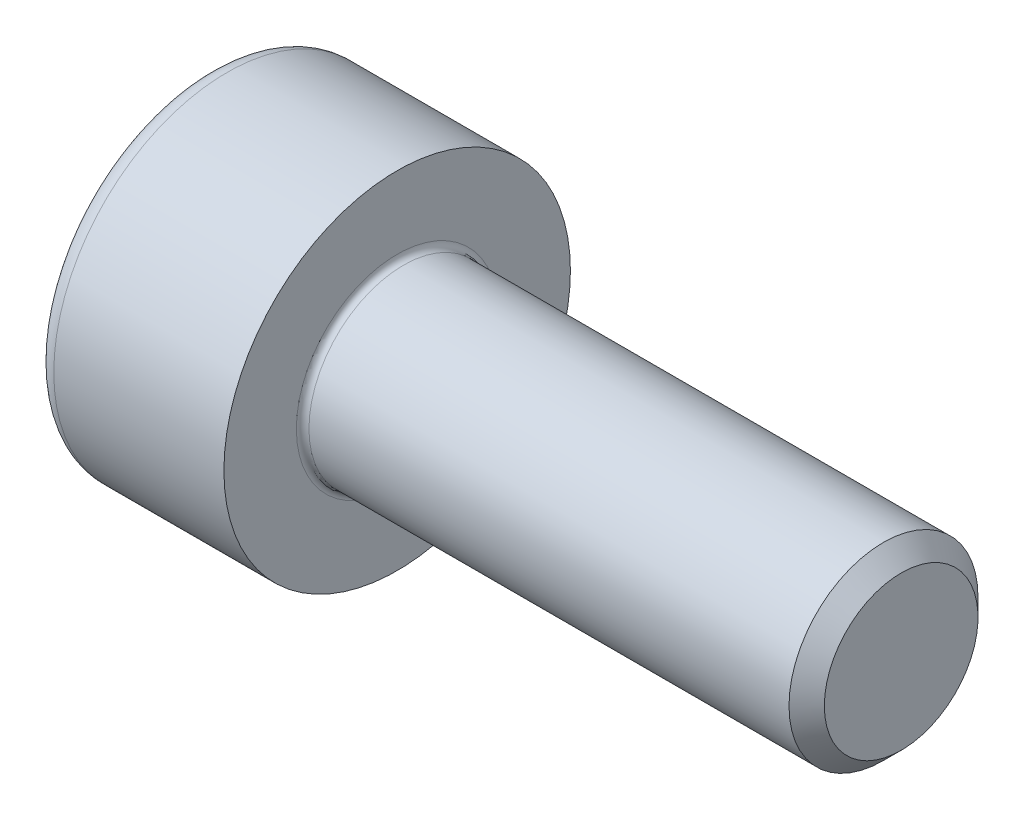
SolidWorks part; units mm, degrees
revolve "Base-Revolve" add sketch "BodySke"
sketch "BodySke" plane through (0, 0, 0) normal (0, 0, 1) x (1, 0, 0)
  line L0 (0, 0) -> (0, 2.75)
  line L1 (0, 2.75) -> (3, 2.75)
  line L2 (3, 2.75) -> (3, 1.5)
  line L3 (3, 1.5) -> (10.7195, 1.5)
  line L4 (11, 1.2195) -> (11, 0)
  line L5 (11, 0) -> (0, 0)
  line L6 (-31.75, 0) -> (127, 0) construction
  line L8 (11, 1.2195) -> (10.7195, 1.5)
  line L10 (11, -1.2195) -> (10.7195, -1.5) construction
  line L11 (3.5, 9.525) -> (3.5, 3.175) construction
  line L12 (3, 9.525) -> (3, 3.175) construction
  line L13 (-49, 9.525) -> (-49, 3.175) construction
  dimension "Head_ht" = 3
  dimension "Length" = 8
  dimension "Body_ch_ang" = 45
  dimension "Diameter" = 3
  dimension "Minor_dia" = 2.439
  dimension "Advance" = 0.5
  dimension "Thread_nom" = 8
  dimension "Thread_length" = 60
  dimension "Head_dia" = 5.5
cosmetic thread "ThreadCosmetic"
fillet "Fillet1" radius 0.1 1 edges at (3, 0, 1.5)
fillet "Fillet2" radius 0.3 1 edges at (0, 0, 2.75)
ref_plane "Plane1" through (0, 0, 0) normal (0, 0, 1) x (1, 0, 0)
ref_plane "Plane2" through (0, 0, 0) normal (0, 1, 0) x (1, 0, 0)
ref_plane "Plane3" through (0, 0, 0) normal (1, 0, 0) x (0, 0, -1)
sketch "Sketch2" plane through (0, 0, 0) normal (0, 0, 1) x (1, 0, 0)
  line L0 (0, 1.26) -> (1.3, 1.26)
  line L1 (1.3, 1.26) -> (2.0275, 0)
  line L2 (-31.75, 0) -> (127, 0) construction
  line L3 (2.0275, 0) -> (0, 0)
  line L4 (0, 0) -> (0, 1.26)
  line L6 (0, 0) -> (47.625, 0) construction
  dimension "D1" = 1.26
  dimension "D2" = 60
  dimension "Depth" = 1.3
revolve "Hex-PreBroach" cut sketch "Sketch2" angle 360 about L6
sketch "Sketch3" plane through (0, 0, 0) normal (-1, 0, 0) x (0, 0.5, 0.866)
  line L0 (0.7275, 1.26) -> (-0.7275, 1.26)
  line L1 (-0.7275, 1.26) -> (-1.4549, 0)
  line L2 (0.7275, 1.26) -> (1.4549, 0)
  line L3 (0.7275, -1.26) -> (1.4549, 0)
  line L4 (0.7275, -1.26) -> (-0.7275, -1.26)
  line L5 (-0.7275, -1.26) -> (-1.4549, 0)
  dimension "D1" = 1.26
  dimension "D2" = 1.26
  dimension "Hex_size" = 2.52
extrude "Hex" cut sketch "Sketch3" against normal blind 1.3
sketch "ThdSchSke" plane through (0, 0, 0) normal (0, 0, 1) x (1, 0, 0)
  line L0 (4.5, -1.2195) -> (4.3036, -1.5)
  line L1 (4.5, -1.2195) -> (4.6964, -1.5)
  line L2 (4.6964, -1.5) -> (4.6964, -1.875)
  line L3 (-3.175, 0) -> (5.1513, 0) construction
  line L4 (0, 2.45) -> (0, -2.45) construction
  line L5 (4.6964, -1.875) -> (4.3036, -1.875)
  line L6 (4.3036, -1.875) -> (4.3036, -1.5)
  dimension "Thread_minor" = 2.439
  dimension "Diameter" = 3
  dimension "Start" = 4.5
revolve "ThreadSchematic" [suppressed] cut sketch "ThdSchSke" angle 360 about L3
pattern_linear "ThdSchPat" [suppressed]
equation "\"D2@Sketch3\" = \"Hex_size@Sketch3\" / 2"
equation "\"D1@Sketch3\" = \"Hex_size@Sketch3\" / 2"
equation "\"D1@Sketch2\" = \"Hex_size@Sketch3\" / 2"
equation "\"Thread_minor@ThreadCosmetic\"  =  \"Minor_dia@BodySke\""
equation "\"Depth@Sketch2\" =  \"Key_eng@Hex\""
equation "\"Thread_length@ThreadCosmetic\" = ((sgn( (\"Length@BodySke\" - \"Advance@BodySke\" * 3.0) - \"Thread_nom@BodySke\" )-1)*( (\"Length@BodySke\" - \"Advance@BodySke\" * 3.0) - \"Thread_nom@BodySke\" ))/-2+ \"Thread_nom@BodySke\""
equation "\"Thread_minor@ThdSchSke\" = \"Minor_dia@BodySke\""
equation "\"Diameter@ThdSchSke\" = \"Diameter@BodySke\""
equation "\"Overcut@ThdSchSke\" = \"Diameter@BodySke\" * 1.25"
equation "\"Start@ThdSchSke\" = \"Head_ht@BodySke\" + \"Length@BodySke\" - \"Thread_length@ThreadCosmetic\"  '---Non-countersunk---"
equation "\"Num_threads@ThdSchPat\" = int( \"Thread_length@ThreadCosmetic\" / \"Advance@BodySke\" + 0.999 )  + 1"
equation "\"Advance@ThdSchPat\" = \"Thread_length@ThreadCosmetic\" /  (\"Num_threads@ThdSchPat\" - 1) 'relax it"
equation "\"Num_threads@ThdSchPat\" = \"Num_threads@ThdSchPat\" - sgn( \"Num_threads@ThdSchPat\" - 1) '---chamfered tips only---"
